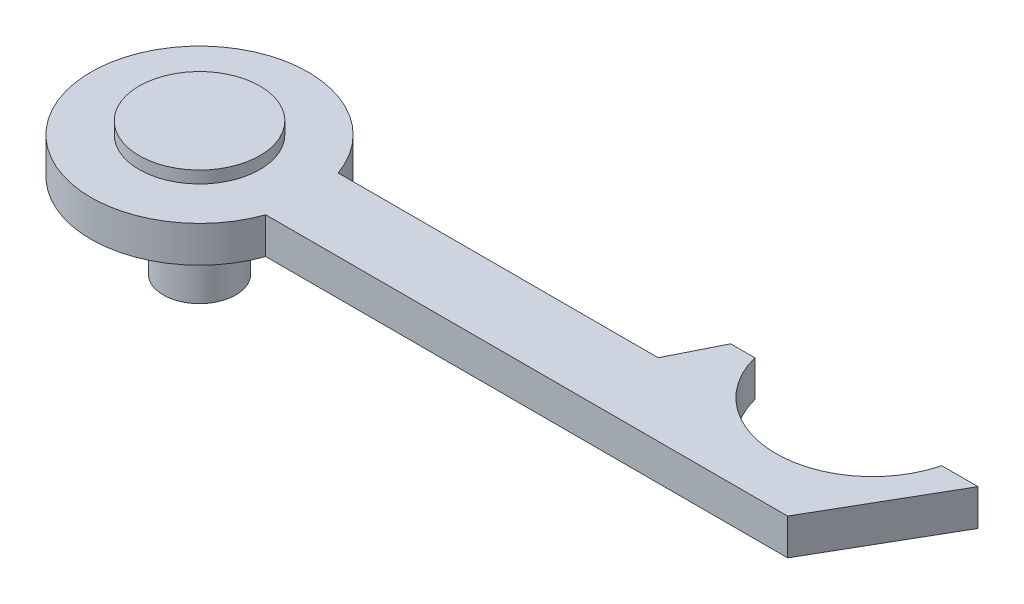
SolidWorks part; units mm, degrees
ref_plane "Ön Düzlem" through (0, 0, 0) normal (0, 0, 1) x (1, 0, 0)
ref_plane "Üst Düzlem" through (0, 0, 0) normal (0, 1, 0) x (1, 0, 0)
ref_plane "Sağ Düzlem" through (0, 0, 0) normal (1, 0, 0) x (0, 0, -1)
sketch "Çizim1" plane through (0, 0, 0) normal (0, 1, 0) x (1, 0, 0)
  circle A0 centre (0, 0) radius 9
  circle A1 centre (0, 0) radius 3
  dimension "D1" = 18
  dimension "D2" = 6
extrude "Yükseklik-Ekstrüzyon1" add sketch "Çizim1" along normal blind 3
sketch "Çizim3" plane through (0, 3, 0) normal (0, 1, 0) x (1, 0, 0)
  line L0 (0, 0) -> (43.7803, 0) construction
  line L1 (8.4853, 3) -> (35, 3)
  line L2 (35, 3) -> (37, 7)
  line L3 (37, 7) -> (39, 7)
  line L4 (54.4919, 7) -> (57.4919, 7)
  line L5 (57.4919, 7) -> (51.7184, -3)
  line L6 (51.7184, -3) -> (8.4853, -3)
  arc A0 (39, 7) -> (54.4919, 7) centre (46.746, 9) ccw
  circle A1 centre (0, 0) radius 9 construction
  arc A2 (8.4853, -3) -> (8.4853, 3) centre (0, 0) ccw
  dimension "D1" = 3
  dimension "D6" = 8
  dimension "D10" = 9
  dimension "D2" = 35
  dimension "D3" = 4
  dimension "D4" = 3
  dimension "D5" = 120
  dimension "D7" = 2
  dimension "D8" = 2
  dimension "D9" = 3
extrude "Yükseklik-Ekstrüzyon2" add sketch "Çizim3" against normal blind 3
sketch "Çizim5" plane through (0, 0, 0) normal (0, 0, 1) x (1, 0, 0)
  line L0 (0, 3) -> (0, -7)
  line L1 (3, 3) -> (-3, 3) construction
  line L2 (0, 3) -> (0, 4)
  line L3 (0, 4) -> (5, 4)
  line L4 (5, 4) -> (5, 3)
  line L5 (8.4853, 3) -> (-9, 3) construction
  line L6 (5, 3) -> (3, 3)
  line L7 (3, 3) -> (3, -7)
  line L8 (3, -7) -> (0, -7)
  dimension "D1" = 1
  dimension "D2" = 5
  dimension "D3" = 3
  dimension "D4" = 10
revolve "Döndür1" add sketch "Çizim5" angle 360 about L0
